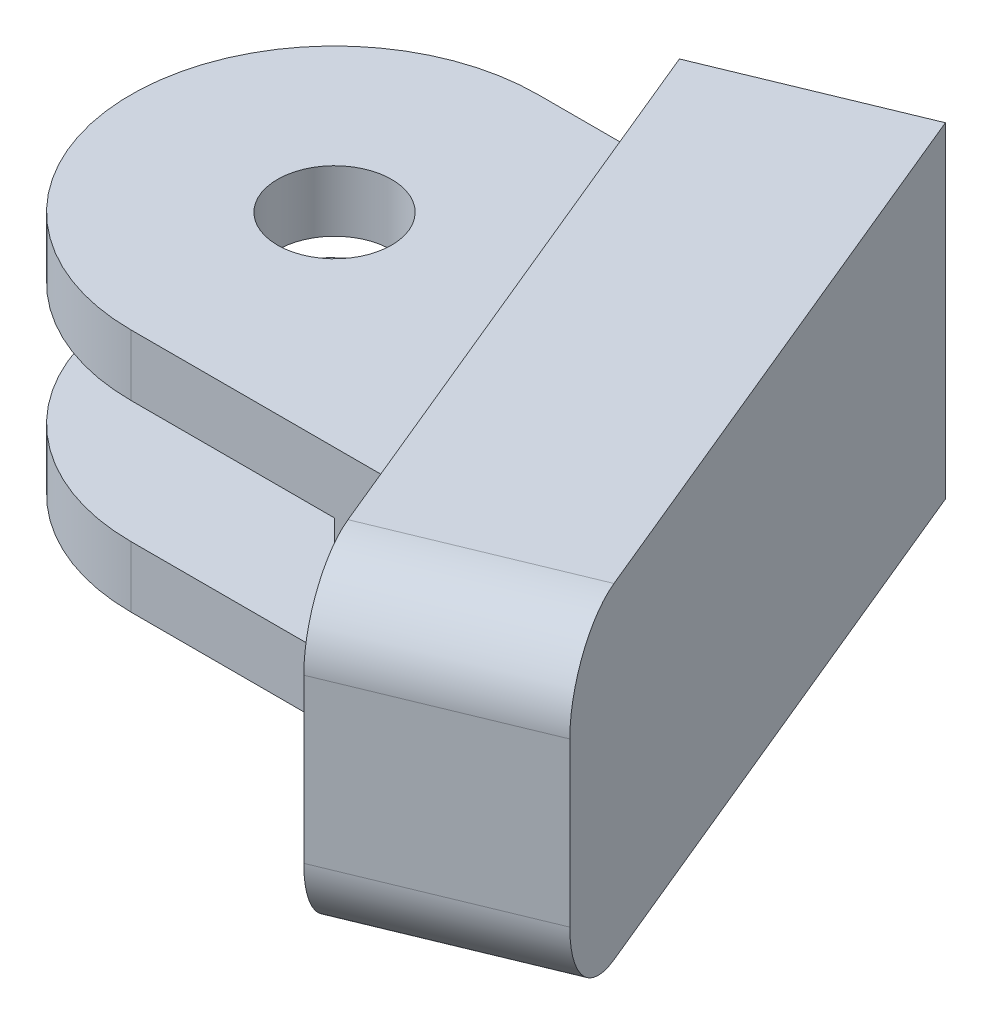
SolidWorks part; units mm, degrees
ref_plane "Front Plane" through (0, 0, 0) normal (0, 0, 1) x (1, 0, 0)
ref_plane "Top Plane" through (0, 0, 0) normal (0, 1, 0) x (1, 0, 0)
ref_plane "Right Plane" through (0, 0, 0) normal (1, 0, 0) x (0, 0, -1)
sketch "Sketch1" plane through (0, 0, 0) normal (0, 0, 1) x (1, 0, 0)
  line L0 (0, 3) -> (0, 1.5)
  line L1 (0, -1.5) -> (0, -3)
  arc A0 (0, -1.5) -> (0, 1.5) centre (0, 0) ccw
  arc A1 (0, -3) -> (0, 3) centre (0, 0) ccw
  dimension "D1" = 1.5
  dimension "D2" = 3
extrude "Boss-Extrude1" add sketch "Sketch1" along normal mid plane 10
ref_plane "Plane1" through (0, 1.5, 0) normal (0, 1, 0) x (1, 0, 0)
sketch "Sketch2" plane through (0, 1.5, 0) normal (0, 1, 0) x (1, 0, 0)
  circle A0 centre (-5, 0) radius 5
  circle A1 centre (-5, 0) radius 1.4
  dimension "D2" = 2.8
  dimension "D3" = 10
  dimension "D1" = 5
extrude "Boss-Extrude2" add sketch "Sketch2" along normal blind 1.5 separate body
sketch "Sketch4" plane through (0, 0, 0) normal (-1, 0, 0) x (0, 0, 1)
  line L1 (-5, 1.5) -> (5, 1.5)
  line L2 (-5, 1.5) -> (-5, 3)
  line L3 (-5, 3) -> (5, 3)
  line L4 (5, 1.5) -> (5, 3)
extrude "Boss-Extrude3" add sketch "Sketch4" along normal up to body separate body
sketch "Sketch5" plane through (0, 0, 0) normal (-1, 0, 0) x (0, 0, 1)
  line L1 (-5, -3) -> (5, -3)
  line L2 (-5, -3) -> (-5, -1.5)
  line L3 (-5, -1.5) -> (5, -1.5)
  line L4 (5, -3) -> (5, -1.5)
ref_plane "Plane2" through (0, -1.5, 0) normal (0, 1, 0) x (1, 0, 0)
sketch "Sketch6" plane through (0, -1.5, 0) normal (0, 1, 0) x (1, 0, 0)
  circle A0 centre (-5, 0) radius 1.4
  circle A1 centre (-5, 0) radius 5
  dimension "D1" = 2.8
  dimension "D2" = 10
extrude "Boss-Extrude4" add sketch "Sketch6" against normal blind 1.5 separate body
extrude "Boss-Extrude5" add sketch "Sketch5" along normal up to body separate body
ref_plane "Plane3" through (1.8, 0, 0) normal (1, 0, 0) x (0, 0, -1)
ref_plane "Piano1" through (0, 0, 0) normal (-1, 0, 0) x (0, 0, 1)
sketch "Schizzo1" plane through (0, 0, 0) normal (-1, 0, 0) x (0, 0, 1)
  line L1 (-5, 3) -> (5, 3)
  line L2 (-5, 3) -> (-5, -3)
  line L3 (-5, -3) -> (5, -3)
  line L4 (5, 3) -> (5, -3)
extrude "Estrusione-Estrusione2" add sketch "Schizzo1" against normal blind 11
sketch "Schizzo2" plane through (0, -3, 0) normal (0, -1, 0) x (1, 0, 0)
  line L0 (3, -5) -> (7.1309, 5)
  line L1 (-5, -5) -> (11, -5) construction
  line L2 (-5, 5) -> (11, 5) construction
  line L3 (7.1309, 5) -> (11, 5)
  line L4 (11, 5) -> (13.562, 5)
  line L5 (13.562, 5) -> (13.562, -5)
  line L6 (13.562, -5) -> (3, -5)
extrude "Taglio-Estrusione1" cut sketch "Schizzo2" against normal blind 11
sketch "Schizzo3" plane through (4.3271, 0, -1.7875) normal (0.9242, 0, -0.3818) x (-0.3818, 0, -0.9242)
  line L0 (-7.3438, 3) -> (3.4758, 3) construction
  line L1 (-7.8438, 4) -> (7.1562, 4)
  line L2 (-9.8438, 2) -> (-9.8438, -2)
  line L3 (-7.8438, -4) -> (7.1562, -4)
  line L4 (7.1562, 4) -> (7.1562, -4)
  line L5 (-7.3438, 3) -> (-7.3438, -3) construction
  arc A0 (-7.8438, -4) -> (-9.8438, -2) centre (-7.8438, -2) cw
  arc A1 (-9.8438, 2) -> (-7.8438, 4) centre (-7.8438, 2) cw
  point P10 (-9.8438, -4)
  point P13 (-9.8438, 4)
  dimension "D5" = 2
  dimension "D1" = 8
  dimension "D2" = 1
  dimension "D3" = 17
  dimension "D4" = 2.5
extrude "Estrusione-Estrusione3" add sketch "Schizzo3" against normal blind 5
sketch "Schizzo4" plane through (0, 1.5, 0) normal (0, -1, 0) x (1, 0, 0)
  circle A0 centre (-5, 0) radius 6
  dimension "D1" = 12
extrude "Taglio-Estrusione2" cut sketch "Schizzo4" along normal up to surface (3 mm away) up to face at (-3.482, -1.5, 0.1667)
